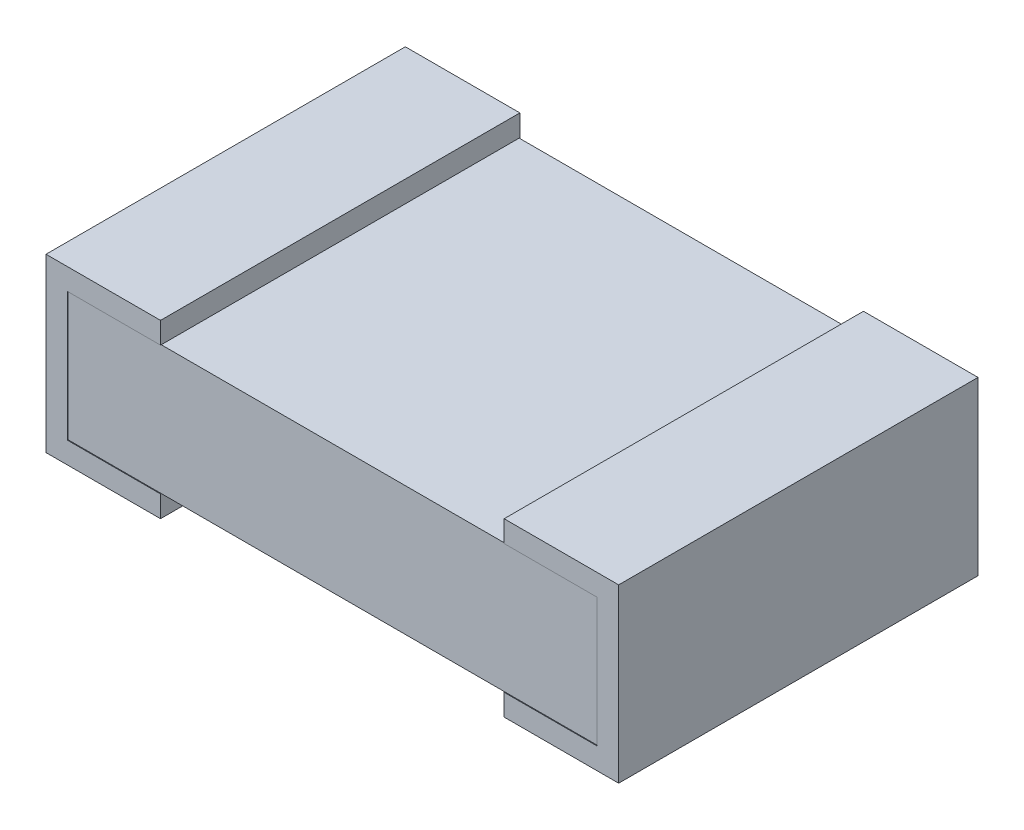
SolidWorks part; units mm, degrees
ref_plane "Front Plane" through (0, 0, 0) normal (0, 0, 1) x (1, 0, 0)
ref_plane "Top Plane" through (0, 0, 0) normal (0, 1, 0) x (1, 0, 0)
ref_plane "Right Plane" through (0, 0, 0) normal (1, 0, 0) x (0, 0, -1)
sketch "Sketch1" plane through (0, 0, 0) normal (0, 0, 1) x (1, 0, 0)
  line L0 (1.9558, 0.0762) -> (0.0762, 0.0762)
  line L1 (1.9558, 0.0762) -> (1.9558, 0.5334)
  line L2 (0.0762, 0.5334) -> (1.9558, 0.5334)
  line L3 (0.0762, 0.5334) -> (0.0762, 0.0762)
  dimension "D1" = 1.8796
  dimension "D2" = 0.4572
  dimension "D3" = 0.0762
  dimension "D4" = 0.0762
extrude "Base-Extrude" add sketch "Sketch1" against normal mid plane 1.27
ref_plane "Plane1" through (0, 0, -0.6375) normal (0, 0, -1) x (-1, 0, 0)
sketch "Sketch2" plane through (0, 0, -0.6375) normal (0, 0, -1) x (-1, 0, 0)
  line L0 (0, 0) -> (-0.4064, 0)
  line L1 (0, 0) -> (0, 0.6096)
  line L2 (0, 0.6096) -> (-0.4064, 0.6096)
  line L3 (-0.4064, 0.6096) -> (-0.4064, 0.5334)
  line L4 (-1.9558, 0.5334) -> (-0.0762, 0.5334) construction
  line L5 (-0.4064, 0) -> (-0.4064, 0.0762)
  line L6 (-0.0762, 0.0762) -> (-1.9558, 0.0762) construction
  line L7 (-0.0762, 0.5334) -> (-0.0762, 0.0762) construction
  line L8 (-0.0762, 0.0762) -> (-0.4064, 0.0762)
  line L9 (-0.4064, 0.5334) -> (-0.0762, 0.5334)
  line L10 (-0.0762, 0.5334) -> (-0.0762, 0.0762)
  dimension "D1" = 0.4064
  dimension "D2" = 0.4064
  dimension "D3" = 0.0762
extrude "Boss-Extrude1" add sketch "Sketch2" against normal blind 1.2751
ref_plane "Board Surface" through (1.016, 0, 0) normal (1, 0, 0) x (0, 0, -1)
mirror "Mirror1" about plane through (1.016, 0, 0) normal (1, 0, 0) of "Boss-Extrude1"
sketch "Component_Outline" plane through (0, 0, 0) normal (0, 1, 0) x (1, 0, 0)
  line L1 (0, 0.6375) -> (2.032, 0.6375)
  line L2 (0, 0.6375) -> (0, -0.6375)
  line L3 (0, -0.6375) -> (2.032, -0.6375)
  line L4 (2.032, 0.6375) -> (2.032, -0.6375)
sketch "Sketch3" plane through (0, 0, 0) normal (0, -1, 0) x (1, 0, 0)
  line L0 (2.032, 0.6375) -> (2.032, -0.6375) construction
  line L1 (0, 0.6375) -> (0, -0.6375) construction
  line L2 (2.032, 0.6375) -> (2.032, -0.6375)
  line L3 (0, 0.6375) -> (0, -0.6375)
  line L4 (0, 0.6375) -> (2.032, -0.6375) construction
  line L5 (0, -0.6375) -> (2.032, 0.6375) construction
  point P4 (1.016, 0)
